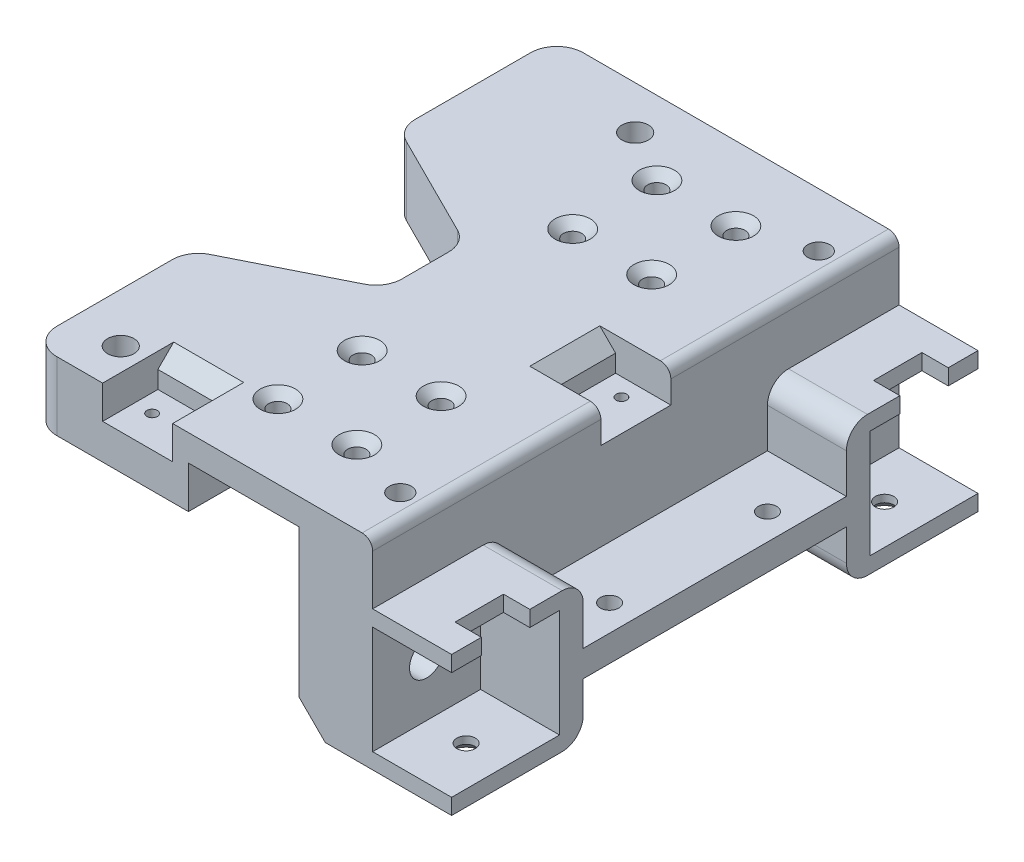
SolidWorks part; units mm, degrees
ref_plane "Front Plane" through (0, 0, 0) normal (0, 0, 1) x (1, 0, 0)
ref_plane "Top Plane" through (0, 0, 0) normal (0, 1, 0) x (1, 0, 0)
ref_plane "Right Plane" through (0, 0, 0) normal (1, 0, 0) x (0, 0, -1)
sketch "Sketch1" plane through (0, 0, 0) normal (0, 1, 0) x (1, 0, 0)
  line L0 (0, 50) -> (0, -50) construction
  line L1 (-10.5, 50) -> (10.5, 50)
  line L2 (-10.5, 50) -> (-10.5, -50)
  line L3 (-10.5, -50) -> (10.5, -50)
  line L5 (-10.5, 50) -> (10.5, -50) construction
  line L6 (-10.5, -50) -> (10.5, 50) construction
  line L7 (-7.5, 36) -> (7.5, 36) construction
  line L8 (-7.5, 36) -> (7.5, 20) construction
  line L9 (-10.5, 0) -> (10, 0) construction
  line L10 (-7.5, -36) -> (7.5, -20) construction
  line L11 (-7.5, -36) -> (7.5, -36) construction
  line L12 (-7.5, 20) -> (7.5, 20) construction
  line L14 (10.5, 50) -> (10.5, -50)
  circle A0 centre (-7.5, 36) radius 1.75
  circle A1 centre (7.5, 36) radius 1.75
  circle A2 centre (-7.5, 20) radius 1.75
  circle A3 centre (7.5, 20) radius 1.75
  circle A4 centre (7.5, -20) radius 1.75
  circle A5 centre (-7.5, -20) radius 1.75
  circle A6 centre (7.5, -36) radius 1.75
  circle A7 centre (-7.5, -36) radius 1.75
  point P0 (0, 0)
  point P16 (0, 36)
  point P27 (0, 0)
  point P29 (10.5, 50.0167)
  point P30 (11, 50)
  point P31 (0, 0)
  dimension "D2" = 3.5
  dimension "D1" = 21
  dimension "D3" = 15
  dimension "D4" = 16
  dimension "D5" = 100
  dimension "D6" = 20
extrude "Boss-Extrude1" add sketch "Sketch1" along normal blind 5
sketch "Sketch2" plane through (10.5, 0, 0) normal (1, 0, 0) x (0, 0, -1)
  line L0 (50, 5) -> (50, 0) construction
  line L1 (-50, 5) -> (50, 5)
  line L2 (-50, 5) -> (-50, -33)
  line L3 (-50, -33) -> (50, -33)
  line L5 (50, 5) -> (50, -33)
  line L8 (-50, 5) -> (50, 5) construction
  point P4 (50, 5)
  point P6 (-50, 5)
  dimension "D1" = 38
extrude "Boss-Extrude2" add sketch "Sketch2" along normal blind 14
sketch "Sketch3" plane through (24.5, 0, 0) normal (1, 0, 0) x (0, 0, -1)
  line L0 (0, 5) -> (0, -33) construction
  line L1 (-25, -18) -> (25, -18)
  line L2 (-25, -18) -> (-25, -23)
  line L3 (-25, -23) -> (25, -23)
  line L4 (25, -18) -> (25, -23)
  line L5 (50, 5) -> (-50, 5) construction
  line L6 (-50, -33) -> (50, -33) construction
  point P10 (0, -18)
  dimension "D1" = 5
  dimension "D2" = 50
  dimension "D3" = 10
extrude "Boss-Extrude3" add sketch "Sketch3" along normal blind 15
sketch "Sketch4" plane through (0, -18, 0) normal (0, 1, 0) x (1, 0, 0)
  line L0 (29.5, 0) -> (39.5, 0) construction
  line L2 (39.5, 25) -> (39.5, -25) construction
  line L3 (34.5, -15) -> (34.5, 15) construction
  circle A0 centre (34.5, 15) radius 1.75
  circle A1 centre (34.5, -15) radius 1.75
  point P8 (34.5, 0)
  dimension "D1" = 30
  dimension "D2" = 3.5
  dimension "D3" = 10
extrude "Cut-Extrude1" cut sketch "Sketch4" against normal through all
sketch "Sketch8" plane through (24.5, 0, 0) normal (1, 0, 0) x (0, 0, -1)
  line L0 (-50, 5) -> (-50, -33) construction
  line L1 (-50, -6.5) -> (-25, -6.5)
  line L2 (-50, -6.5) -> (-50, -9.5)
  line L3 (-50, -33) -> (-25, -33)
  line L4 (-25, -6.5) -> (-25, -33)
  line L5 (-50, -30) -> (-50, -33)
  line L6 (-50, -30) -> (-29.5, -30)
  line L8 (-50, -9.5) -> (-29.5, -9.5)
  line L9 (-29.5, -30) -> (-29.5, -9.5)
  line L10 (0, 2.75) -> (0, -2.75) construction
  line L11 (29.5, -30) -> (29.5, -9.5)
  line L12 (50, -9.5) -> (29.5, -9.5)
  line L13 (50, -30) -> (29.5, -30)
  line L14 (50, -30) -> (50, -33)
  line L15 (25, -6.5) -> (25, -33)
  line L16 (50, -33) -> (25, -33)
  line L17 (50, -6.5) -> (50, -9.5)
  line L18 (50, -6.5) -> (25, -6.5)
  line L19 (-50, -33) -> (50, -33) construction
  line L20 (-25, -18) -> (-25, -23) construction
  dimension "D1" = 3
  dimension "D3" = 3
  dimension "D4" = 20.5
  dimension "D5" = 20.5
extrude "Boss-Extrude6" add sketch "Sketch8" along normal blind 15
sketch "Sketch9" plane through (24.5, 0, 0) normal (1, 0, 0) x (0, 0, -1)
  line L0 (-50, -9.5) -> (-29.5, -30) construction
  line L1 (50, -9.5) -> (29.5, -30) construction
  line L3 (50, -30) -> (50, -9.5) construction
  circle A0 centre (-39.75, -19.75) radius 3.25
  circle A1 centre (39.75, -19.75) radius 3.25
  point P12 (0, 0)
  point P13 (-50, -9.5)
  point P15 (50, -9.5)
  point P17 (0, 0)
  dimension "D1" = 6.5
extrude "Cut-Extrude3" cut sketch "Sketch9" against normal through all
sketch "Sketch10" plane through (10.5, 0, 0) normal (-1, 0, 0) x (0, 0, 1)
  circle A0 centre (-39.75, -19.75) radius 5.25
  circle A1 centre (39.75, -19.75) radius 5.25
  dimension "D1" = 10.5
extrude "Cut-Extrude4" cut sketch "Sketch10" against normal offset from surface (9 mm away) 5 up to face at (24.5, -19.75, 36.5)
sketch "Sketch11" plane through (0, -6.5, 0) normal (0, 1, 0) x (1, 0, 0)
  line L0 (39.5, -25) -> (39.5, -50) construction
  line L1 (39.5, -35.15) -> (34.5, -35.15)
  line L2 (39.5, -35.15) -> (39.5, -44.35)
  line L3 (39.5, -44.35) -> (34.5, -44.35)
  line L4 (34.5, -35.15) -> (34.5, -44.35)
  line L5 (34.5, -39.75) -> (39.5, -39.75) construction
  line L7 (-10.5, 0) -> (39.5, 0) construction
  line L8 (-10.5, 50) -> (-10.5, -50) construction
  line L9 (39.5, 25) -> (39.5, -25) construction
  line L10 (39.5, -35.15) -> (34.5, -35.15)
  line L11 (39.5, -44.35) -> (34.5, -44.35)
  line L12 (34.5, 39.75) -> (39.5, 39.75) construction
  line L13 (39.5, 44.35) -> (34.5, 44.35)
  line L14 (39.5, 35.15) -> (34.5, 35.15)
  line L15 (34.5, 35.15) -> (34.5, 44.35)
  line L16 (39.5, 44.35) -> (34.5, 44.35)
  line L17 (39.5, 35.15) -> (39.5, 44.35)
  line L18 (39.5, 35.15) -> (34.5, 35.15)
  line L19 (39.5, -50) -> (39.5, -29.5) construction
  point P22 (39.5, -39.75)
  line M7 (39.5, -50) -> (39.5, -25)
  dimension "D1" = 9.2
  dimension "D3" = 5
extrude "Cut-Extrude5" cut sketch "Sketch11" against normal up to next contours L1 L4 L3 M7 | L14 L17 L13 L15
sketch "Sketch12" plane through (0, -30, 0) normal (0, 1, 0) x (1, 0, 0)
  line L0 (39.5, -39.75) -> (24.5, -39.75) construction
  line L1 (39.5, -29.5) -> (39.5, -50) construction
  line L2 (24.5, -25) -> (24.5, -50) construction
  line L3 (-20.9, 0) -> (20.9, 0) construction
  circle A0 centre (32, -39.75) radius 1.75
  circle A2 centre (32, 39.75) radius 1.75
  dimension "D1" = 3.5
extrude "Cut-Extrude6" cut sketch "Sketch12" against normal through all
sketch "Sketch13" plane through (-10.5, 0, 0) normal (-1, 0, 0) x (0, 0, 1)
  line L0 (-50, 5) -> (-50, 0) construction
  line L1 (-50, 5) -> (50, 5)
  line L2 (-50, 5) -> (-50, -8)
  line L3 (-50, -8) -> (50, -8)
  line L4 (50, 5) -> (50, -8)
  point P4 (0, 0)
  point P5 (-50, 5)
  point P10 (0, 0)
  point P11 (50, 5)
  dimension "D1" = 13
extrude "Boss-Extrude7" add sketch "Sketch13" along normal blind 30
sketch "Sketch14" plane through (0, 5, 0) normal (0, 1, 0) x (1, 0, 0)
  line L0 (39.5, -25) -> (39.5, -35.15) construction
  line L5 (-24.725, -42.205) -> (-24.725, 50) construction
  line L6 (-24.095, 41.8075) -> (-24.095, -50) construction
  line L7 (39.5, -35.15) -> (34.5, -35.15) construction
  line L12 (-17.4375, 35.15) -> (39.5, 35.15) construction
  line L18 (-31.15, -35.78) -> (39.5, -35.78) construction
  line L20 (-40.5, -50) -> (24.5, -50) construction
  line L21 (0, 50) -> (0, -50) construction
  line L22 (24.5, 50) -> (-40.5, 50) construction
  line L23 (-10, 50) -> (-10, -50) construction
  circle A0 centre (-17.4375, 41.8075) radius 2.5
  circle A1 centre (-31.15, -42.205) radius 2.5
  circle A2 centre (-31.15, -42.205) radius 6.425 construction
  circle A3 centre (-17.4375, 41.8075) radius 6.6575 construction
  point P18 (-28.575, 50)
  point P24 (-10.8712, 50)
  point P30 (0, 0)
  dimension "D1" = 5
  dimension "D2" = 5
  dimension "D4" = 12.85
  dimension "D5" = 13.315
  dimension "D6" = 0.63
  dimension "D7" = 10
  dimension "D3" = 0.63
  dimension "D8" = 21.15
extrude "Cut-Extrude7" cut sketch "Sketch14" against normal through all
sketch "Sketch15" plane through (0, -8, 0) normal (0, -1, 0) x (1, 0, 0)
  line L0 (-40.5, -50) -> (-40.5, 50) construction
  line L1 (-27.05, 44.5721) -> (-31.15, 46.9393)
  line L2 (-31.15, 46.9393) -> (-35.25, 44.5721)
  line L3 (-35.25, 44.5721) -> (-35.25, 39.8379)
  line L4 (-35.25, 39.8379) -> (-31.15, 37.4707)
  line L5 (-31.15, 37.4707) -> (-27.05, 39.8379)
  line L6 (-27.05, 39.8379) -> (-27.05, 44.5721)
  line L7 (-13.3375, -44.1746) -> (-13.3375, -39.4404)
  line L8 (-13.3375, -39.4404) -> (-17.4375, -37.0732)
  line L9 (-17.4375, -37.0732) -> (-21.5375, -39.4404)
  line L10 (-21.5375, -39.4404) -> (-21.5375, -44.1746)
  line L11 (-21.5375, -44.1746) -> (-17.4375, -46.5418)
  line L12 (-17.4375, -46.5418) -> (-13.3375, -44.1746)
  circle A0 centre (-31.15, 42.205) radius 4.1 construction
  circle A1 centre (-17.4375, -41.8075) radius 4.1 construction
  dimension "D1" = 8.2
extrude "Cut-Extrude8" cut sketch "Sketch15" against normal blind 5
sketch "Sketch16" plane through (0, 5, 0) normal (0, 1, 0) x (1, 0, 0)
  line L0 (19.5, 39.75) -> (39.5, 39.75) construction
  line L1 (39.5, 39.75) -> (39.5, -39.75) construction
  line L2 (39.5, -39.75) -> (19.5, -39.75) construction
  line L3 (19.5, -39.75) -> (19.5, 39.75) construction
  line L4 (39.5, 50) -> (39.5, 29.5) construction
  line L5 (39.5, -29.5) -> (39.5, -50) construction
  circle A0 centre (19.5, 39.75) radius 2.1
  circle A1 centre (19.5, -39.75) radius 2.1
  dimension "D1" = 4.2
  dimension "D2" = 4.2
  dimension "D3" = 20
extrude "Cut-Extrude9" cut sketch "Sketch16" against normal blind 4
chamfer "Chamfer1" distance 1.6 angle 45 8 edges at (7.5, 5, 34.25) (-7.5, 5, 34.25) (7.5, 5, 18.25) (-7.5, 5, 18.25) (7.5, 5, -18.25) (-7.5, 5, -18.25) (7.5, 5, -34.25) (-7.5, 5, -34.25)
sketch "Sketch17" plane through (0, 5, 0) normal (0, 1, 0) x (1, 0, 0)
  line L0 (-40.5, 20) -> (-15.5, 7.5)
  line L1 (-40.5, -50) -> (-40.5, 50) construction
  line L2 (-15.5, 7.5) -> (-15.5, -7.5)
  line L3 (-15.5, -7.5) -> (-40.5, -20)
  line L4 (-40.5, -20) -> (-40.5, 20)
  point P5 (-15.5, 0)
  dimension "D1" = 15
  dimension "D2" = 25
  dimension "D3" = 40
extrude "Cut-Extrude10" cut sketch "Sketch17" against normal through all
chamfer "Chamfer2" distance 1.6 angle 45 2 edges at (32, -33, -41.5) (32, -33, 41.5)
chamfer "Chamfer3" distance 5 angle 45 1 edges at (10.5, -33, 0)
sketch "Sketch18" plane through (0, 1, 0) normal (0, 1, 0) x (1, 0, 0)
  circle A0 centre (19.5, 39.75) radius 1.75
  circle A1 centre (19.5, -39.75) radius 1.75
  dimension "D1" = 3.5
  dimension "D2" = 3.5
extrude "Cut-Extrude11" cut sketch "Sketch18" against normal blind 4
fillet "Fillet1" radius 5 6 edges at (-40.5, -1.5, 50) (-40.5, -1.5, 20) (-15.5, -1.5, 7.5) (-15.5, -1.5, -7.5) (-40.5, -1.5, -20) (-40.5, -1.5, -50)
fillet "Fillet2" radius 4 4 edges at (32, -33, -25) (32, -6.5, -25) (32, -33, 25) (32, -6.5, 25)
sketch "Sketch19" plane through (24.5, 0, 0) normal (1, 0, 0) x (0, 0, -1)
  line L0 (50, 5) -> (-50, 5) construction
  line L1 (-6.65, 5) -> (6.65, 5)
  line L2 (-6.65, 5) -> (-6.65, -1.3)
  line L3 (-6.65, -1.3) -> (6.65, -1.3)
  line L4 (6.65, 5) -> (6.65, -1.3)
  point P7 (0, 5)
  dimension "D1" = 13.3
  dimension "D2" = 6.3
extrude "Cut-Extrude12" cut sketch "Sketch19" against normal blind 10.5
sketch "Sketch20" plane through (0, -1.3, 0) normal (0, 1, 0) x (1, 0, 0)
  line L0 (18.5, 3.25) -> (18.5, -3.25) construction
  line L3 (14, 6.65) -> (14, -6.65) construction
  line L4 (17.5, 3.25) -> (17.5, -3.25) construction
  circle A0 centre (18.5, 3.25) radius 1
  circle A1 centre (18.5, -3.25) radius 1
  point P2 (14, 0)
  point P3 (18.5, 0)
  dimension "D1" = 2
  dimension "D2" = 6.5
  dimension "D3" = 3.5
extrude "Cut-Extrude13" cut sketch "Sketch20" against normal blind 3
chamfer "Chamfer4" distance 3 angle 45 1 edges at (14, 5, 0)
fillet "Fillet3" radius 2 2 edges at (24.5, 5, 28.325) (24.5, 5, -28.325)
sketch "Sketch22" plane through (0, 5, 0) normal (0, 1, 0) x (1, 0, 0)
  line L1 (-26.8, -50) -> (-13.5, -50)
  line L2 (-26.8, -50) -> (-26.8, -39.5)
  line L3 (-26.8, -39.5) -> (-13.5, -39.5)
  line L4 (-13.5, -50) -> (-13.5, -39.5)
  line L5 (-10.5, 50) -> (-10.5, -50) construction
  line L7 (-35.5, -50) -> (22.5, -50) construction
  point P10 (0, 0)
  dimension "D1" = 10.5
  dimension "D2" = 13.3
  dimension "D3" = 3
extrude "Cut-Extrude14" cut sketch "Sketch22" against normal blind 6.3
sketch "Sketch23" plane through (0, -1.3, 0) normal (0, 1, 0) x (1, 0, 0)
  line L0 (-13.5, -39.5) -> (-26.8, -39.5) construction
  line L3 (-23.4, -44) -> (-16.9, -44) construction
  line L5 (-26.8, -50) -> (-13.5, -50) construction
  circle A3 centre (-23.4, -44) radius 1
  circle A4 centre (-16.9, -44) radius 1
  point P11 (-20.15, -50)
  point P12 (-20.15, -44)
  dimension "D1" = 2
  dimension "D2" = 4.5
  dimension "D3" = 2
  dimension "D4" = 6.5
extrude "Cut-Extrude15" cut sketch "Sketch23" against normal blind 3
chamfer "Chamfer5" distance 3 angle 45 1 edges at (-20.15, 5, 39.5)
